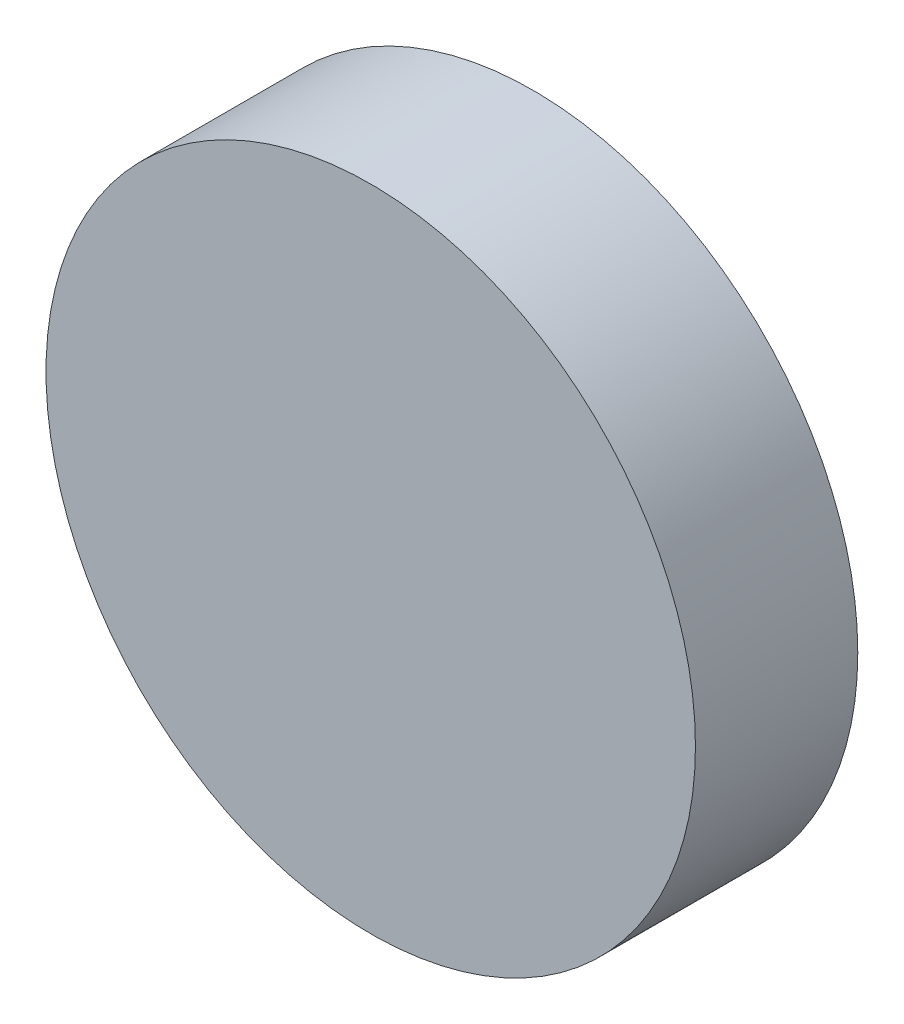
SolidWorks part; units mm, degrees
ref_plane "Front Plane" through (0, 0, 0) normal (0, 0, 1) x (1, 0, 0)
ref_plane "Top Plane" through (0, 0, 0) normal (0, 1, 0) x (1, 0, 0)
ref_plane "Right Plane" through (0, 0, 0) normal (1, 0, 0) x (0, 0, -1)
sketch "Sketch1" plane through (0, 0, 0) normal (0, 0, 1) x (1, 0, 0)
  circle A0 centre (0, 0) radius 4
  dimension "D1" = 8
extrude "Boss-Extrude1" add sketch "Sketch1" along normal blind 2
